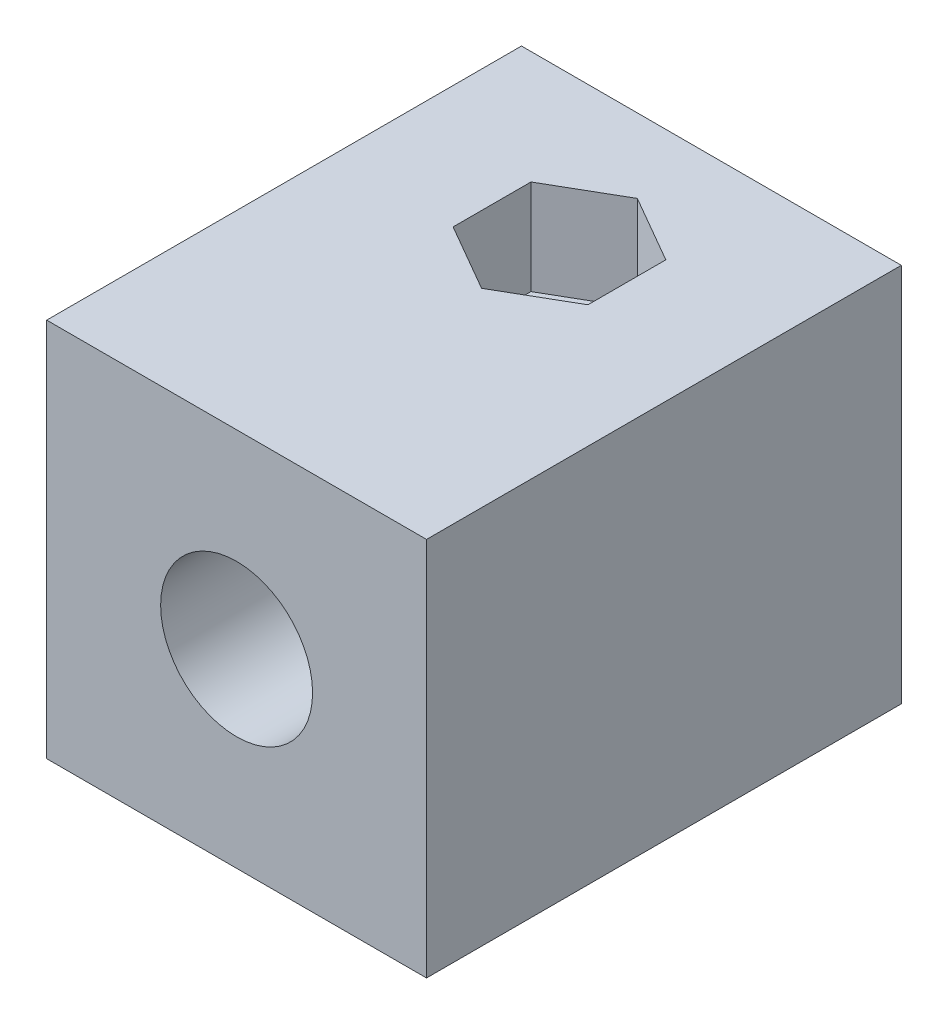
SolidWorks part; units mm, degrees
ref_plane "Спереди" through (0, 0, 0) normal (0, 0, 1) x (1, 0, 0)
ref_plane "Сверху" through (0, 0, 0) normal (0, 1, 0) x (1, 0, 0)
ref_plane "Справа" through (0, 0, 0) normal (1, 0, 0) x (0, 0, -1)
sketch "Sketch1" plane through (0, 0, 0) normal (0, 1, 0) x (1, 0, 0)
  line L1 (10, -12.5) -> (-10, -12.5)
  line L2 (10, -12.5) -> (10, 12.5)
  line L3 (10, 12.5) -> (-10, 12.5)
  line L4 (-10, -12.5) -> (-10, 12.5)
  line L5 (10, -12.5) -> (-10, 12.5) construction
  line L6 (10, 12.5) -> (-10, -12.5) construction
  point P0 (0, 0)
  dimension "D1" = 20
  dimension "D2" = 25
extrude "Boss-Extrude1" add sketch "Sketch1" along normal blind 20
sketch "Sketch2" plane through (0, 0, 12.5) normal (0, 0, 1) x (1, 0, 0)
  line L0 (0, 20) -> (0, 0) construction
  line L1 (-10, 20) -> (10, 20) construction
  line L2 (-10, 0) -> (10, 0) construction
  circle A0 centre (0, 10) radius 4
  dimension "D1" = 8
extrude "Cut-Extrude1" cut sketch "Sketch2" against normal blind 20
sketch "Sketch3" plane through (0, 20, 0) normal (0, 1, 0) x (1, 0, 0)
  line L0 (0, -12.5) -> (0, 12.5) construction
  line L1 (-10, -12.5) -> (10, -12.5) construction
  line L2 (10, 12.5) -> (-10, 12.5) construction
  circle A0 centre (0, 4.5) radius 1.5
  dimension "D1" = 3
  dimension "D2" = 8
extrude "Cut-Extrude2" cut sketch "Sketch3" against normal through all
sketch "Sketch4" plane through (0, 20, 0) normal (0, 1, 0) x (1, 0, 0)
  line L1 (0, 8.6) -> (-3.5507, 6.55)
  line L2 (-3.5507, 6.55) -> (-3.5507, 2.45)
  line L3 (-3.5507, 2.45) -> (0, 0.4)
  line L4 (0, 0.4) -> (3.5507, 2.45)
  line L5 (3.5507, 2.45) -> (3.5507, 6.55)
  line L6 (3.5507, 6.55) -> (0, 8.6)
  line L7 (10, -12.5) -> (10, 12.5) construction
  circle A0 centre (0, 4.5) radius 4.1 construction
  point P11 (0, 8.6)
  dimension "D1" = 8.2
extrude "Cut-Extrude3" cut sketch "Sketch4" against normal blind 5
